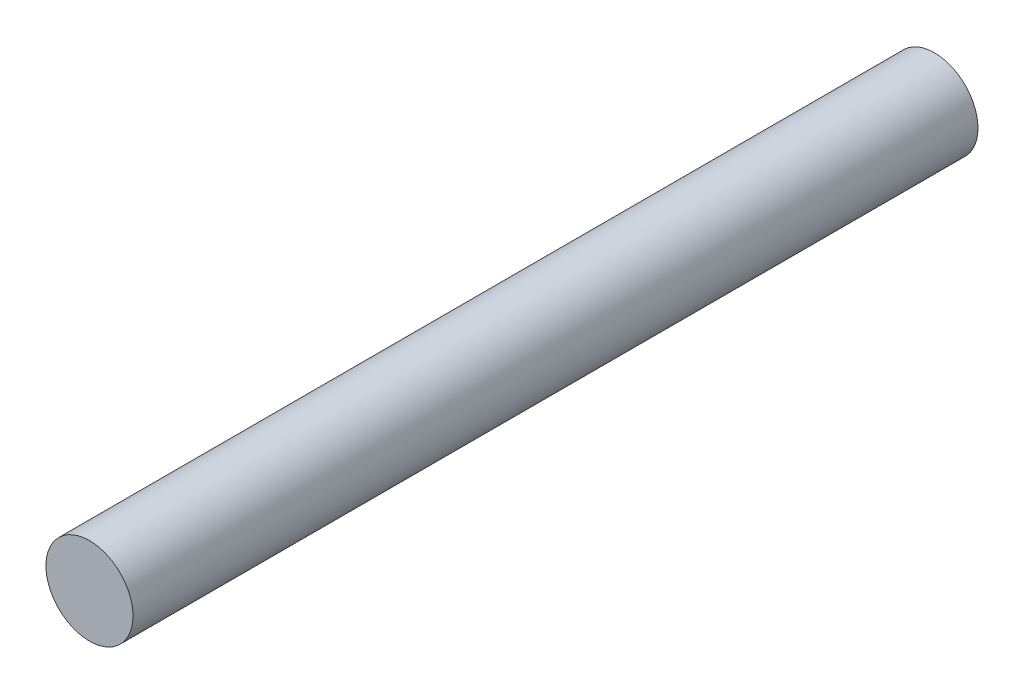
SolidWorks part; units mm, degrees
ref_plane "Front Plane" through (0, 0, 0) normal (0, 0, 1) x (1, 0, 0)
ref_plane "Top Plane" through (0, 0, 0) normal (0, 1, 0) x (1, 0, 0)
ref_plane "Right Plane" through (0, 0, 0) normal (1, 0, 0) x (0, 0, -1)
sketch "Sketch1" plane through (0, 0, 0) normal (0, 0, 1) x (1, 0, 0)
  circle A0 centre (0, 0) radius 3.175
extrude "Boss-Extrude1" add sketch "Sketch1" along normal blind 61.595
